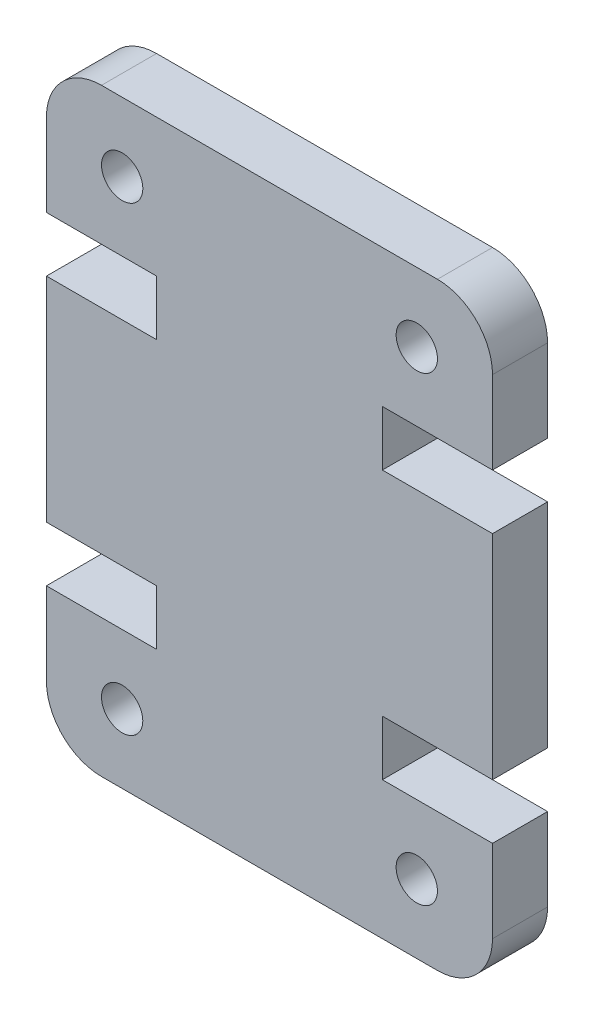
SolidWorks part; units mm, degrees
ref_plane "Front Plane" through (0, 0, 0) normal (0, 0, 1) x (1, 0, 0)
ref_plane "Top Plane" through (0, 0, 0) normal (0, 1, 0) x (1, 0, 0)
ref_plane "Right Plane" through (0, 0, 0) normal (1, 0, 0) x (0, 0, -1)
sketch "Sketch1" plane through (0, 0, 0) normal (0, 0, 1) x (1, 0, 0)
  line L0 (0, 14.74) -> (0, 7)
  line L1 (16.2, 2) -> (16.2, 5)
  line L2 (12.2, 5) -> (16.2, 5)
  line L3 (2, 0) -> (14.2, 0)
  line L4 (16.2, 7) -> (12.2, 7)
  line L5 (12.2, 7) -> (12.2, 5)
  line L6 (16.2, 14.74) -> (16.2, 7)
  line L7 (4, 7) -> (4, 5)
  line L8 (0, 19.74) -> (0, 16.74)
  line L9 (4, 16.74) -> (0, 16.74)
  line L10 (0, 7) -> (4, 7)
  line L11 (0, 14.74) -> (4, 14.74)
  line L12 (4, 5) -> (0, 5)
  line L13 (4, 14.74) -> (4, 16.74)
  line L14 (12.2, 14.74) -> (12.2, 16.74)
  line L15 (16.2, 14.74) -> (12.2, 14.74)
  line L16 (0, 2) -> (0, 5)
  line L17 (2, 21.74) -> (14.2, 21.74)
  line L18 (12.2, 16.74) -> (16.2, 16.74)
  line L19 (16.2, 19.74) -> (16.2, 16.74)
  line L20 (8.1, 21.74) -> (8.1, 0) construction
  line L21 (0, 10.87) -> (16.2, 10.87) construction
  circle A0 centre (13.45, 2.5) radius 0.75
  arc A1 (16.2, 2) -> (14.2, 0) centre (14.2, 2) cw
  circle A2 centre (2.75, 19.24) radius 0.75
  arc A3 (0, 2) -> (2, 0) centre (2, 2) ccw
  arc A4 (0, 19.74) -> (2, 21.74) centre (2, 19.74) cw
  circle A5 centre (2.75, 2.5) radius 0.75
  arc A6 (16.2, 19.74) -> (14.2, 21.74) centre (14.2, 19.74) ccw
  circle A7 centre (13.45, 19.24) radius 0.75
  point P15 (8.1, 10.87)
  dimension "D1" = 1.5
  dimension "D2" = 2
  dimension "D3" = 2.75
  dimension "D4" = 8.1
  dimension "D5" = 2.5
  dimension "D6" = 5
  dimension "D8" = 10.87
extrude "Boss-Extrude1" add sketch "Sketch1" along normal blind 2
equation "\"D4@Sketch1\"= \"fingerWidth@parametersSketch@prostheticParameters.SLDPRT\" / 2'PIP width"
equation "\"D8@Sketch1\"= ( \"HL@parametersSketch@prostheticParameters.SLDPRT\" * 0.204 - 4 - 12 ) / 2 'PIP length - Sil. Sht MIP - Sil.Sht PIP"
